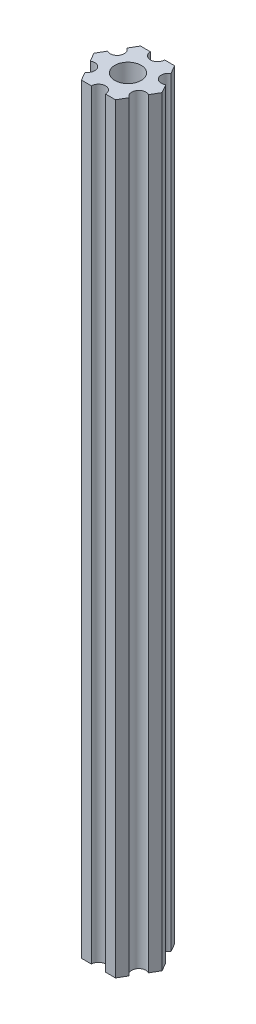
SolidWorks part; units mm, degrees
material "Churro - 6005A-T61"
ref_plane "Plano frontal" through (0, 0, 0) normal (0, 0, 1) x (1, 0, 0)
ref_plane "Plano superior" through (0, 0, 0) normal (0, 1, 0) x (1, 0, 0)
ref_plane "Plano direito" through (0, 0, 0) normal (1, 0, 0) x (0, 0, -1)
ref_plane "Plano1" through (0, 85, 0) normal (0, 1, 0) x (1, 0, 0)
sketch "Esboço1" plane through (0, 85, 0) normal (0, 1, 0) x (1, 0, 0)
  line L0 (6.1627, -1.826) -> (7.2169, 0)
  line L1 (7.2169, 0) -> (6.1627, 1.826)
  line L2 (4.6627, 4.424) -> (3.6084, 6.25)
  line L3 (3.6084, 6.25) -> (1.5, 6.25)
  line L4 (-1.5, 6.25) -> (-3.6084, 6.25)
  line L5 (-3.6084, 6.25) -> (-4.6627, 4.424)
  line L6 (-6.1627, 1.826) -> (-7.2169, 0)
  line L7 (-7.2169, 0) -> (-6.1627, -1.826)
  line L8 (-4.6627, -4.424) -> (-3.6084, -6.25)
  line L9 (-3.6084, -6.25) -> (-1.5, -6.25)
  line L10 (1.5, -6.25) -> (3.6084, -6.25)
  line L11 (3.6084, -6.25) -> (4.6627, -4.424)
  arc A0 (6.1627, 1.826) -> (4.6627, 4.424) centre (5.4127, 3.125) cw
  arc A1 (1.5, 6.25) -> (-1.5, 6.25) centre (0, 6.25) cw
  arc A2 (-4.6627, 4.424) -> (-6.1627, 1.826) centre (-5.4127, 3.125) cw
  arc A3 (-6.1627, -1.826) -> (-4.6627, -4.424) centre (-5.4127, -3.125) cw
  arc A4 (-1.5, -6.25) -> (1.5, -6.25) centre (0, -6.25) cw
  arc A5 (4.6627, -4.424) -> (6.1627, -1.826) centre (5.4127, -3.125) cw
  circle A6 centre (0, 0) radius 2.79
extrude "Ressalto-extrusão1" add sketch "Esboço1" against normal blind 161
